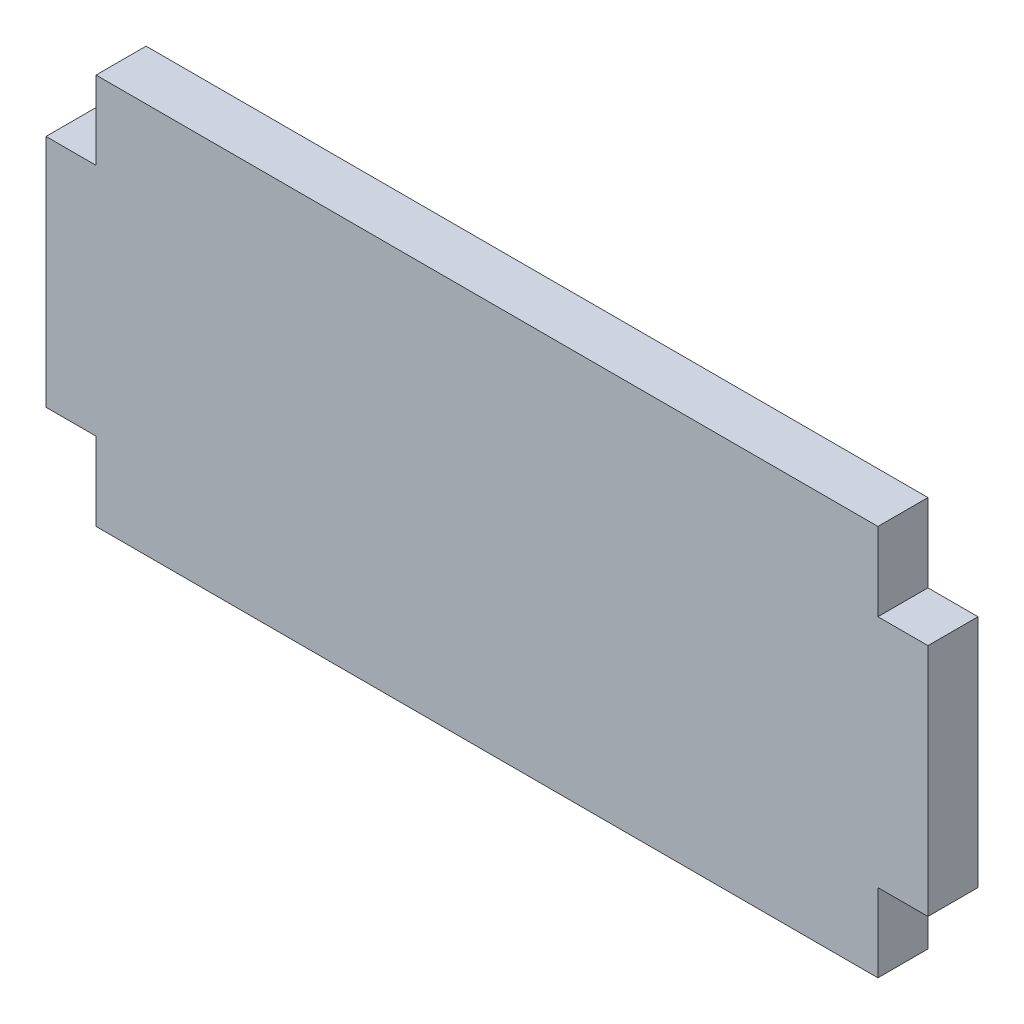
SolidWorks part; units mm, degrees
ref_plane "Front Plane" through (0, 0, 0) normal (0, 0, 1) x (1, 0, 0)
ref_plane "Top Plane" through (0, 0, 0) normal (0, 1, 0) x (1, 0, 0)
ref_plane "Right Plane" through (0, 0, 0) normal (1, 0, 0) x (0, 0, -1)
sketch "Sketch1" plane through (0, 0, 0) normal (0, 0, 1) x (1, 0, 0)
  line L0 (0, 0) -> (0, -15)
  line L1 (0, -15) -> (3.2, -15)
  line L2 (3.2, -15) -> (3.2, -20)
  line L3 (3.2, -20) -> (53.2, -20)
  line L4 (53.2, -20) -> (53.2, -15)
  line L5 (53.2, -15) -> (56.4, -15)
  line L6 (56.4, -15) -> (56.4, 0)
  line L7 (56.4, 0) -> (53.2, 0)
  line L8 (53.2, 0) -> (53.2, 5)
  line L9 (53.2, 5) -> (3.2, 5)
  line L10 (3.2, 5) -> (3.2, 0)
  line L11 (3.2, 0) -> (0, 0)
  dimension "D1" = 3.2
  dimension "D2" = 3.2
  dimension "D3" = 50
  dimension "D4" = 25
  dimension "D5" = 15
extrude "Boss-Extrude1" add sketch "Sketch1" along normal blind 3.2
